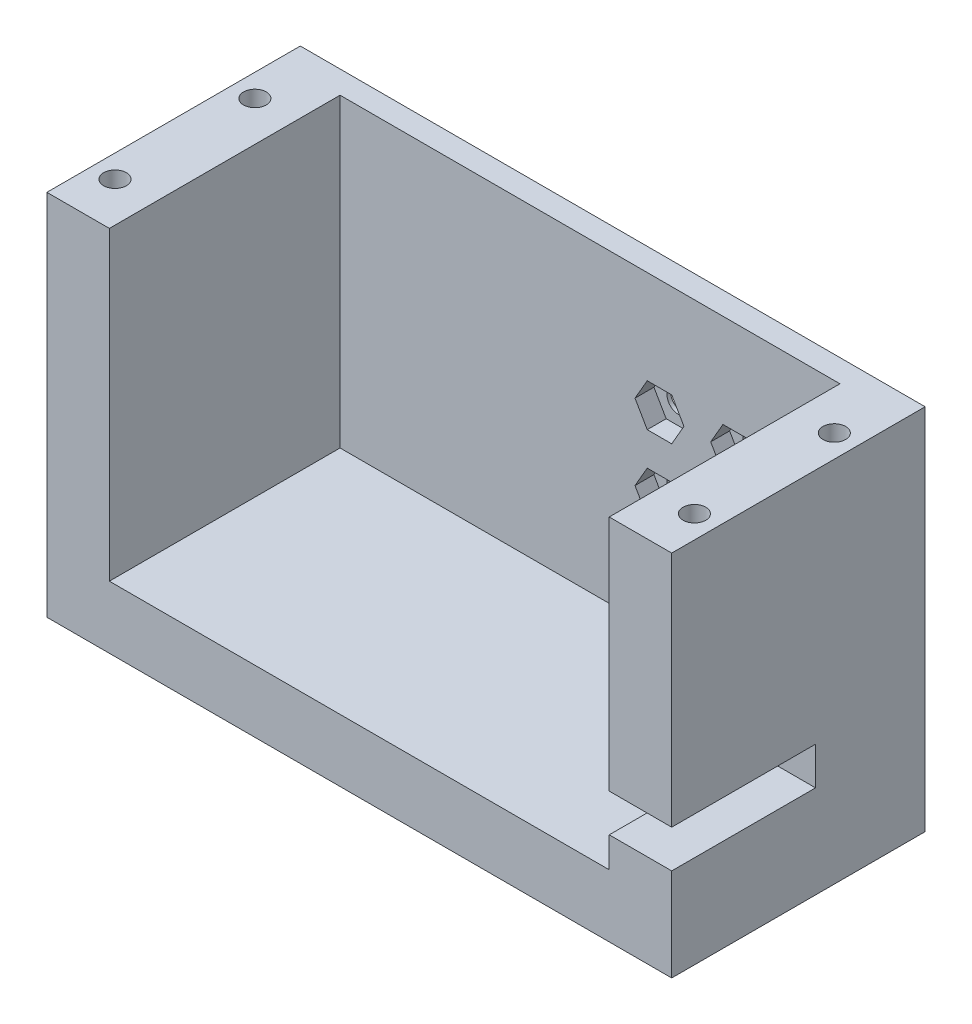
SolidWorks part; units mm, degrees
material "6061 합금"
ref_plane "정면" through (0, 0, 0) normal (0, 0, 1) x (1, 0, 0)
ref_plane "윗면" through (0, 0, 0) normal (0, 1, 0) x (1, 0, 0)
ref_plane "우측면" through (0, 0, 0) normal (1, 0, 0) x (0, 0, -1)
sketch "스케치3" plane through (0, 0, 0) normal (0, 0, 1) x (1, 0, 0)
  line L0 (21517.5223, 8422.8529) -> (21525.7773, 8422.8529)
  line L1 (21600.0723, 8374.2325) -> (21517.5223, 8374.2325)
  line L2 (21600.0723, 8374.2325) -> (21600.0723, 8422.8529)
  line L3 (21525.7773, 8422.8529) -> (21525.7773, 8382.4875)
  line L4 (21517.5223, 8374.2325) -> (21517.5223, 8422.8529)
  line L5 (21525.7773, 8382.4875) -> (21591.8173, 8382.4875)
  line L6 (21591.8173, 8382.4875) -> (21591.8173, 8422.8529)
  line L7 (21591.8173, 8422.8529) -> (21600.0723, 8422.8529)
  dimension "D1" = 8.255
  dimension "D2" = 8.255
  dimension "D3" = 48.6204
  dimension "D4" = 40.3654
  dimension "D5" = 40.3654
  dimension "D6" = 82.55
extrude "보스-돌출1" add sketch "스케치3" along normal blind 30.48
ref_plane "평면1" through (0, 8374.2325, 0) normal (0, -1, 0) x (-1, 0, 0)
sketch "스케치4" plane through (0, 8374.2325, 0) normal (0, -1, 0) x (-1, 0, 0)
  line L0 (-21517.5223, -30.48) -> (-21517.5223, 0) construction
  line L1 (-21517.5223, -30.48) -> (-21600.0723, -30.48) construction
  circle A0 centre (-21576.7175, -15.24) radius 3.302
  point P0 (-21576.7175, -15.24)
  dimension "D3" = 6.604
  dimension "D1" = 59.1951
  dimension "D2" = 15.24
extrude "보스-돌출2" add sketch "스케치4" along normal blind 6.1246
ref_plane "평면2" through (0, 0, 0) normal (0, 0, -1) x (-1, 0, 0)
sketch "스케치5" plane through (0, 0, 0) normal (0, 0, -1) x (-1, 0, 0)
  line L0 (-16.764, 8374.2325) -> (16.764, 8374.2325) construction
  line L1 (-21600.0723, 8422.8529) -> (-21517.5223, 8422.8529)
  line L2 (-21600.0723, 8422.8529) -> (-21600.0723, 8374.2325)
  line L3 (-21600.0723, 8374.2325) -> (-21517.5223, 8374.2325)
  line L4 (-21517.5223, 8422.8529) -> (-21517.5223, 8374.2325)
  line L5 (-21517.5223, 8422.8529) -> (-21517.5223, 8374.2325) construction
extrude "보스-돌출3" add sketch "스케치5" along normal blind 3
ref_plane "평면3" through (0, 0, 0) normal (0, 0, 1) x (1, 0, 0)
sketch "스케치6" plane through (0, 0, 0) normal (0, 0, 1) x (1, 0, 0)
  line L1 (21525.7773, 8422.8529) -> (21525.7773, 8382.4875) construction
  line L2 (21591.8173, 8382.4875) -> (21525.7773, 8382.4875) construction
  line L3 (21517.5223, 8422.8529) -> (21517.5223, 8374.2325) construction
  line L4 (21517.5223, 8402.6725) -> (21600.0723, 8402.6725) construction
  line L5 (21600.0723, 8374.2325) -> (21600.0723, 8422.8529) construction
  circle A1 centre (21577.9766, 8407.6725) radius 1.5
  circle A3 centre (21567.9766, 8407.6725) radius 1.5
  circle A4 centre (21567.9766, 8397.6725) radius 1.5
  circle A6 centre (21577.9766, 8397.6725) radius 1.5
  dimension "D10" = 3
  dimension "D11" = 3
  dimension "D1" = 20.185
  dimension "D2" = 40.3654
  dimension "D3" = 5
  dimension "D6" = 10
  dimension "D7" = 5
extrude "컷-돌출1" cut sketch "스케치6" against normal blind 3
ref_plane "평면4" through (0, 0, 0) normal (0, 0, 1) x (1, 0, 0)
sketch "스케치7" plane through (0, 0, 0) normal (0, 0, 1) x (1, 0, 0)
  line L0 (21569.5932, 8410.4725) -> (21566.36, 8410.4725)
  line L1 (21566.36, 8410.4725) -> (21564.7434, 8407.6725)
  line L2 (21564.7434, 8407.6725) -> (21566.36, 8404.8725)
  line L3 (21566.36, 8404.8725) -> (21569.5932, 8404.8725)
  line L4 (21569.5932, 8404.8725) -> (21571.2097, 8407.6725)
  line L5 (21571.2097, 8407.6725) -> (21569.5932, 8410.4725)
  line L6 (21566.36, 8410.4725) -> (21569.5932, 8404.8725) construction
  line L7 (21569.5932, 8410.4725) -> (21566.36, 8404.8725) construction
  line L8 (21564.7434, 8407.6725) -> (21571.2097, 8407.6725) construction
  line L9 (21569.5932, 8400.4725) -> (21566.36, 8400.4725)
  line L10 (21566.36, 8400.4725) -> (21564.7434, 8397.6725)
  line L11 (21564.7434, 8397.6725) -> (21566.36, 8394.8725)
  line L12 (21566.36, 8394.8725) -> (21569.5932, 8394.8725)
  line L13 (21569.5932, 8394.8725) -> (21571.2097, 8397.6725)
  line L14 (21571.2097, 8397.6725) -> (21569.5932, 8400.4725)
  line L15 (21566.36, 8400.4725) -> (21569.5932, 8394.8725) construction
  line L16 (21569.5932, 8400.4725) -> (21566.36, 8394.8725) construction
  line L17 (21564.7434, 8397.6725) -> (21571.2097, 8397.6725) construction
  line L18 (21579.5932, 8400.4725) -> (21576.36, 8400.4725)
  line L19 (21576.36, 8400.4725) -> (21574.7434, 8397.6725)
  line L20 (21574.7434, 8397.6725) -> (21576.36, 8394.8725)
  line L21 (21576.36, 8394.8725) -> (21579.5932, 8394.8725)
  line L22 (21579.5932, 8394.8725) -> (21581.2097, 8397.6725)
  line L23 (21581.2097, 8397.6725) -> (21579.5932, 8400.4725)
  line L24 (21576.36, 8400.4725) -> (21579.5932, 8394.8725) construction
  line L25 (21579.5932, 8400.4725) -> (21576.36, 8394.8725) construction
  line L26 (21574.7434, 8397.6725) -> (21581.2097, 8397.6725) construction
  line L27 (21579.5932, 8410.4725) -> (21576.36, 8410.4725)
  line L28 (21576.36, 8410.4725) -> (21574.7434, 8407.6725)
  line L29 (21574.7434, 8407.6725) -> (21576.36, 8404.8725)
  line L30 (21576.36, 8404.8725) -> (21579.5932, 8404.8725)
  line L31 (21579.5932, 8404.8725) -> (21581.2097, 8407.6725)
  line L32 (21581.2097, 8407.6725) -> (21579.5932, 8410.4725)
  line L33 (21576.36, 8410.4725) -> (21579.5932, 8404.8725) construction
  line L34 (21579.5932, 8410.4725) -> (21576.36, 8404.8725) construction
  line L35 (21574.7434, 8407.6725) -> (21581.2097, 8407.6725) construction
  circle A0 centre (21567.9766, 8407.6725) radius 1.5
  circle A1 centre (21567.9766, 8397.6725) radius 1.5
  circle A2 centre (21577.9766, 8397.6725) radius 1.5
  circle A3 centre (21577.9766, 8407.6725) radius 1.5
  dimension "D1" = 3.2332
  dimension "D2" = 3.2332
  dimension "D3" = 3.2332
  dimension "D4" = 3.2332
  dimension "D5" = 3.2332
  dimension "D6" = 3.2332
  dimension "D7" = 3.2332
  dimension "D8" = 3.2332
  dimension "D9" = 3.2332
  dimension "D10" = 3.2332
  dimension "D11" = 3.2332
  dimension "D12" = 3.2332
  dimension "D13" = 3.2332
  dimension "D14" = 3.2332
  dimension "D15" = 3.2332
  dimension "D16" = 3.2332
  dimension "D17" = 3.2332
  dimension "D18" = 3.2332
  dimension "D19" = 3.2332
  dimension "D20" = 3.2332
  dimension "D21" = 3.2332
  dimension "D22" = 3.2332
  dimension "D23" = 3.2332
  dimension "D24" = 3.2332
extrude "컷-돌출2" cut sketch "스케치7" against normal blind 2.5
ref_plane "평면5" through (0, 8422.8529, 0) normal (0, 1, 0) x (1, 0, 0)
sketch "스케치8" plane through (0, 8422.8529, 0) normal (0, 1, 0) x (1, 0, 0)
  line L0 (21600.0723, -30.48) -> (21591.8173, -30.48) construction
  line L1 (-30.1098, 0) -> (30.1098, 0) construction
  line L2 (21600.0723, -30.48) -> (21600.0723, 3) construction
  line L3 (21558.7973, 3) -> (21558.7973, -30.48) construction
  line L4 (21517.5223, 3) -> (21600.0723, 3) construction
  line L5 (21591.8173, -30.48) -> (21525.7773, -30.48) construction
  circle A0 centre (21597.0723, -6) radius 1.5
  circle A1 centre (21597.0723, -24.48) radius 1.5
  circle A2 centre (21520.5223, -24.48) radius 1.5
  circle A3 centre (21520.5223, -6) radius 1.5
  point P0 (21597.0723, -24.48)
  point P1 (21597.0723, -6)
  dimension "D5" = 3
  dimension "D6" = 3
  dimension "D1" = 6
  dimension "D2" = 6
  dimension "D3" = 3
  dimension "D4" = 3
extrude "컷-돌출3" cut sketch "스케치8" against normal blind 10
ref_plane "평면6" through (0, 0, 30.48) normal (0, 0, 1) x (1, 0, 0)
sketch "스케치9" plane through (0, 0, 30.48) normal (0, 0, 1) x (1, 0, 0)
  line L1 (21591.8173, 8422.8529) -> (21591.8173, 8382.4875) construction
  line L2 (21591.8173, 8386.4875) -> (21600.0723, 8386.4875)
  line L3 (21591.8173, 8386.4875) -> (21591.8173, 8391.4875)
  line L4 (21591.8173, 8391.4875) -> (21600.0723, 8391.4875)
  line L10 (21600.0723, 8386.4875) -> (21600.0723, 8391.4875)
  line L11 (21600.0723, 8374.2325) -> (21600.0723, 8422.8529) construction
  line L12 (21591.8173, 8382.4875) -> (21525.7773, 8382.4875) construction
  dimension "D2" = 5
  dimension "D3" = 4
extrude "컷-돌출4" cut sketch "스케치9" against normal blind 19
ref_plane "평면7" through (0, 0, 30.48) normal (0, 0, 1) x (1, 0, 0)
